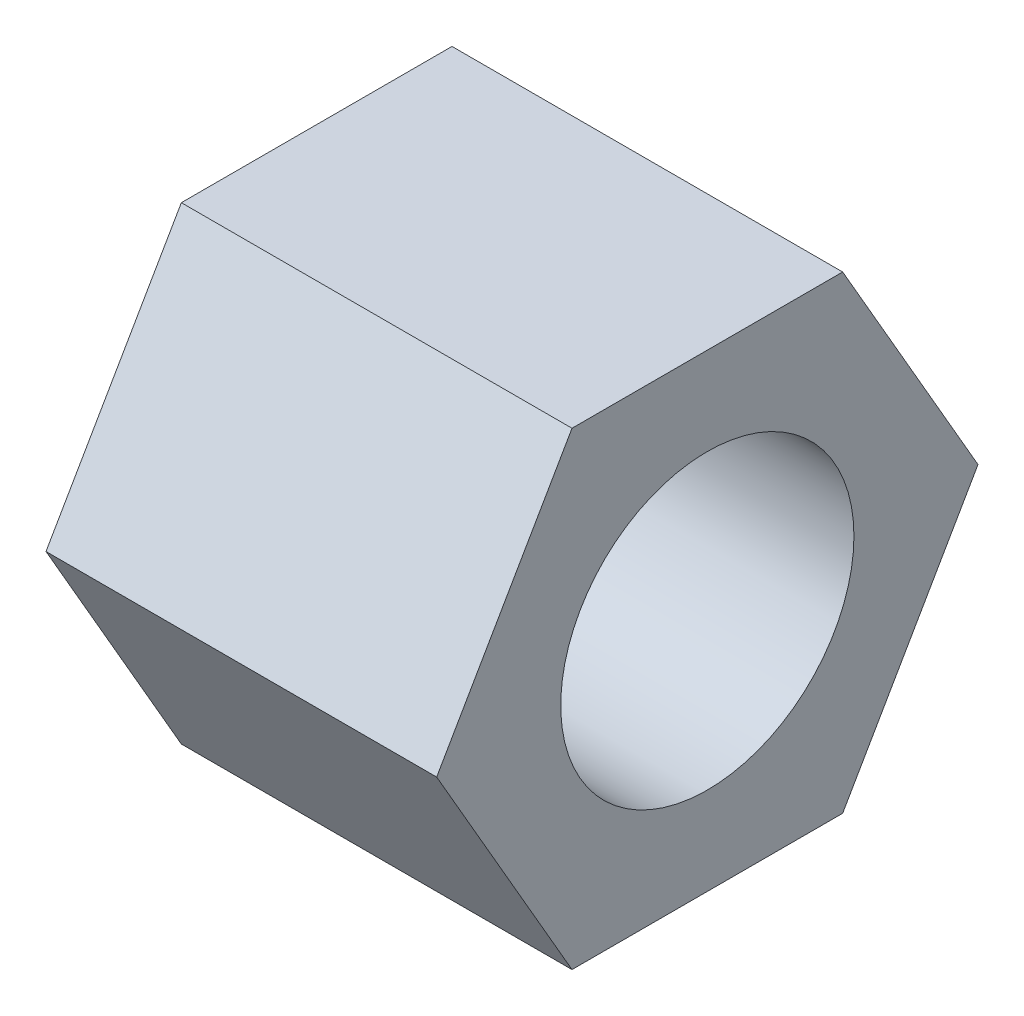
SolidWorks part; units mm, degrees
ref_plane "前视基准面" through (0, 0, 0) normal (0, 0, 1) x (1, 0, 0)
ref_plane "上视基准面" through (0, 0, 0) normal (0, 1, 0) x (1, 0, 0)
ref_plane "右视基准面" through (0, 0, 0) normal (1, 0, 0) x (0, 0, -1)
sketch "草图1" plane through (0, 0, 0) normal (1, 0, 0) x (0, 0, -1)
  line L1 (6.9282, 0) -> (3.4641, 6)
  line L2 (3.4641, 6) -> (-3.4641, 6)
  line L3 (-3.4641, 6) -> (-6.9282, 0)
  line L4 (-6.9282, 0) -> (-3.4641, -6)
  line L5 (-3.4641, -6) -> (3.4641, -6)
  line L6 (3.4641, -6) -> (6.9282, 0)
  circle A0 centre (0, 0) radius 6 construction
  dimension "D1" = 12
extrude "凸台-拉伸1" add sketch "草图1" along normal blind 10
sketch "草图2" plane through (10, 0, 0) normal (1, 0, 0) x (0, 0, -1)
  line L1 (3.7528, 0) -> (1.8764, 3.25) construction
  line L2 (1.8764, 3.25) -> (-1.8764, 3.25) construction
  line L3 (-1.8764, 3.25) -> (-3.7528, 0) construction
  line L4 (-3.7528, 0) -> (-1.8764, -3.25) construction
  line L5 (-1.8764, -3.25) -> (1.8764, -3.25) construction
  line L6 (1.8764, -3.25) -> (3.7528, 0) construction
  circle A0 centre (0, 0) radius 3.25 construction
  circle A1 centre (0, 0) radius 3.7528
  dimension "D1" = 6.5
extrude "切除-拉伸1" cut sketch "草图2" against normal blind 8
sketch "草图3" plane through (2, 0, 0) normal (1, 0, 0) x (0, 0, -1)
  circle A0 centre (0, 0) radius 1.5
extrude "切除-拉伸2" cut sketch "草图3" against normal blind 7
